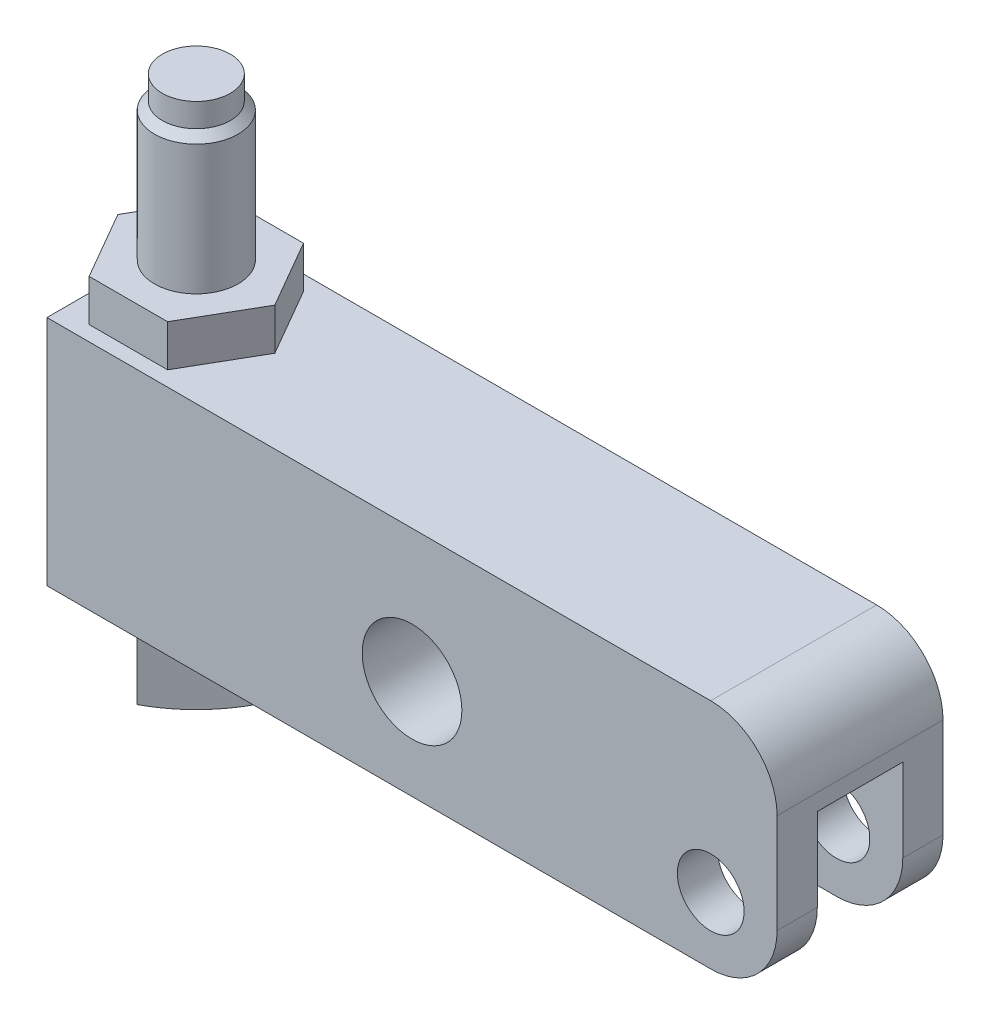
SolidWorks part; units mm, degrees
material "Alloy Steel"
ref_plane "Front Plane" through (0, 0, 0) normal (0, 0, 1) x (1, 0, 0)
ref_plane "Top Plane" through (0, 0, 0) normal (0, 1, 0) x (1, 0, 0)
ref_plane "Right Plane" through (0, 0, 0) normal (1, 0, 0) x (0, 0, -1)
sketch "Sketch11" plane through (0, 0, 0) normal (0, 0, 1) x (1, 0, 0)
  line L1 (-63.5, 15.875) -> (6.35, 15.875)
  line L2 (-63.5, 15.875) -> (-63.5, -6.35)
  line L3 (-63.5, -6.35) -> (6.35, -6.35)
  line L4 (6.35, 15.875) -> (6.35, -6.35)
  circle A0 centre (0, 0) radius 3.194
  circle A1 centre (-28.575, 3.175) radius 4.7689
  dimension "D1" = 6.3881
  dimension "D6" = 9.5377
  dimension "D2" = 6.35
  dimension "D3" = 63.5
  dimension "D4" = 22.225
  dimension "D5" = 28.575
  dimension "D7" = 6.35
  dimension "D8" = 3.175
extrude "Extrude3" add sketch "Sketch11" along normal mid plane 15.875
sketch "Sketch12" plane through (0, -6.35, 0) normal (0, -1, 0) x (1, 0, 0)
  line L0 (0, 0) -> (-16.2248, 0) construction
  line L1 (-7.9248, 4.0894) -> (6.35, 4.0894)
  line L2 (6.35, 7.9375) -> (6.35, -7.9375) construction
  line L3 (6.35, 4.0894) -> (6.35, -4.0894)
  line L4 (-63.5, 7.9375) -> (6.35, 7.9375) construction
  line L5 (-7.9248, -4.0894) -> (6.35, -4.0894)
  arc A0 (-7.9248, 4.0894) -> (-7.9248, -4.0894) centre (-7.9248, 0) ccw
  dimension "D3" = 18.3642
  dimension "D1" = 8.1788
  dimension "D2" = 3.8481
extrude "Cut-Extrude1" cut sketch "Sketch12" against normal blind 14.3002
fillet "Fillet1" radius 6.35 3 edges at (6.35, 15.875, 0) (6.35, -6.35, -6.0134) (6.35, -6.35, 6.0134)
sketch "Sketch13" plane through (0, 15.875, 0) normal (0, 1, 0) x (1, 0, 0)
  line L1 (-49.6417, 0) -> (-53.3958, 6.5024)
  line L2 (-53.3958, 6.5024) -> (-60.9042, 6.5024)
  line L3 (-60.9042, 6.5024) -> (-64.6583, 0)
  line L4 (-64.6583, 0) -> (-60.9042, -6.5024)
  line L5 (-60.9042, -6.5024) -> (-53.3958, -6.5024)
  line L6 (-53.3958, -6.5024) -> (-49.6417, 0)
  circle A0 centre (-57.15, 0) radius 6.5024 construction
  dimension "D1" = 13.0048
  dimension "D2" = 57.15
extrude "Extrude4" add sketch "Sketch13" along normal blind 3.9878
sketch "Sketch14" plane through (0, 0, 0) normal (0, 0, 1) x (1, 0, 0)
  line L0 (-57.15, 48.4817) -> (-57.15, -12.9942) construction
  line L1 (-49.6417, 19.8628) -> (-49.6417, 15.875) construction
  line L2 (-64.6583, 19.8628) -> (-64.6583, 15.875) construction
  line L3 (-60.4012, 33.02) -> (-60.4012, 35.2806)
  line L4 (-60.4012, 33.02) -> (-61.1505, 32.2707)
  line L5 (-61.1505, 32.2707) -> (-61.1505, -6.985)
  line L6 (-61.1505, -6.985) -> (-72.4613, -6.985)
  line L7 (-72.4613, -6.985) -> (-72.4613, -7.747)
  line L8 (-60.4012, 35.2806) -> (-57.15, 35.2806)
  line L9 (-57.15, 35.2806) -> (-57.15, -14.986)
  line L10 (-63.5, -6.35) -> (0, -6.35) construction
  arc A0 (-72.4613, -7.747) -> (-57.15, -14.986) centre (-57.15, 4.826) ccw
  dimension "D5" = 19.812
  dimension "D2" = 6.5024
  dimension "D3" = 45
  dimension "D4" = 40.005
  dimension "D6" = 8.636
  dimension "D7" = 8.001
  dimension "D8" = 0.762
  dimension "D9" = 8.001
  dimension "D10" = 57.15
  dimension "D11" = 2.2606
revolve "Revolve2" add sketch "Sketch14" angle 360 about L0
sketch "Sketch15" plane through (0, -6.985, 0) normal (0, 1, 0) x (1, 0, 0)
  line L0 (-51.4924, 0) -> (-62.8076, 0) construction
  line L1 (-57.15, 5.6576) -> (-62.8076, 0)
  line L2 (-62.8076, 0) -> (-57.15, -5.6576)
  line L3 (-57.15, -5.6576) -> (-51.4924, 0)
  line L4 (-51.4924, 0) -> (-57.15, 5.6576)
  circle A0 centre (-57.15, 0) radius 4.0005 construction
  circle A1 centre (-57.15, 0) radius 15.3113 construction
  circle A2 centre (-57.15, 0) radius 15.3113
  dimension "D1" = 8.001
extrude "Cut-Extrude2" cut sketch "Sketch15" against normal through all
